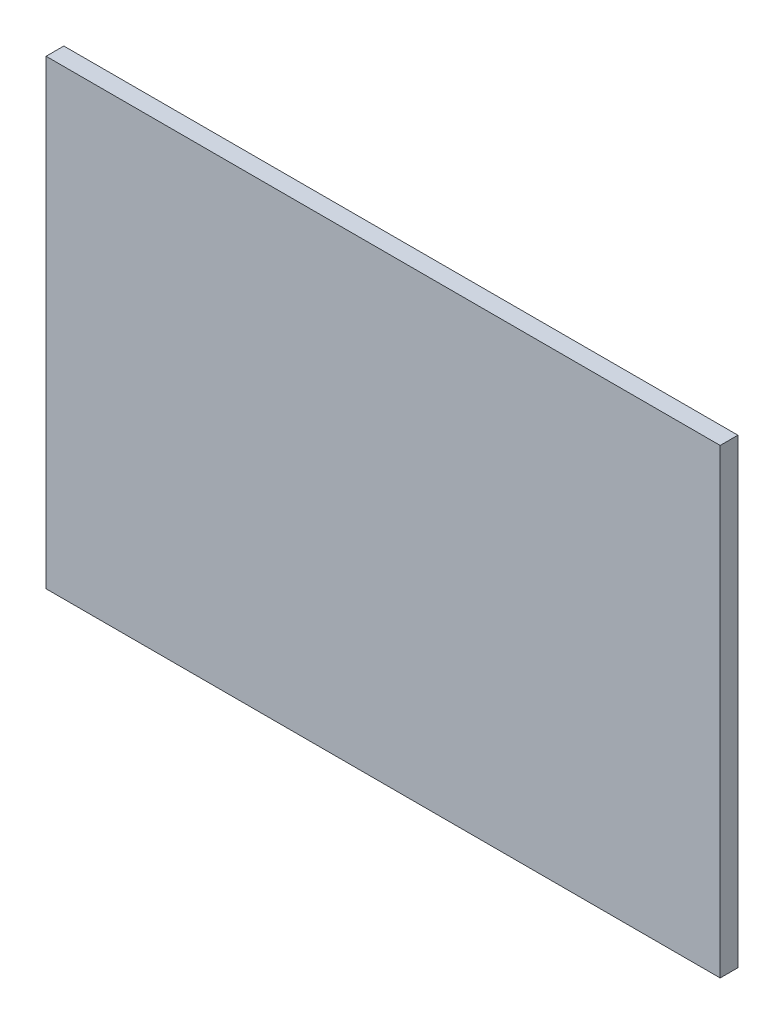
SolidWorks part; units mm, degrees
ref_plane "Front Plane" through (0, 0, 0) normal (0, 0, 1) x (1, 0, 0)
ref_plane "Top Plane" through (0, 0, 0) normal (0, 1, 0) x (1, 0, 0)
ref_plane "Right Plane" through (0, 0, 0) normal (1, 0, 0) x (0, 0, -1)
sketch "Sketch1" plane through (0, 0, 0) normal (0, 0, 1) x (1, 0, 0)
  line L1 (0, 0) -> (38, 0)
  line L2 (0, 0) -> (0, 26)
  line L3 (0, 26) -> (38, 26)
  line L4 (38, 0) -> (38, 26)
  dimension "D1" = 26
  dimension "D2" = 38
extrude "Boss-Extrude1" add sketch "Sketch1" along normal blind 1
